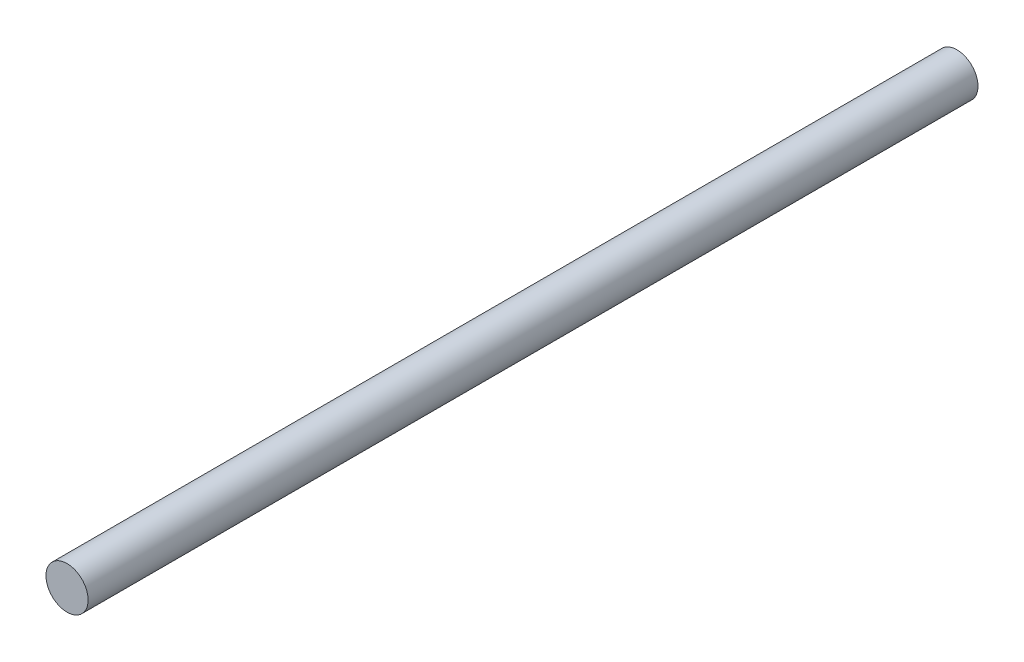
SolidWorks part; units mm, degrees
ref_plane "Front Plane" through (0, 0, 0) normal (0, 0, 1) x (1, 0, 0)
ref_plane "Top Plane" through (0, 0, 0) normal (0, 1, 0) x (1, 0, 0)
ref_plane "Right Plane" through (0, 0, 0) normal (1, 0, 0) x (0, 0, -1)
sketch "Sketch1" plane through (0, 0, 0) normal (0, 0, 1) x (1, 0, 0)
  circle A0 centre (0, 0) radius 11.43
  dimension "D1" = 22.86
extrude "Boss-Extrude1" add sketch "Sketch1" along normal blind 482.6
